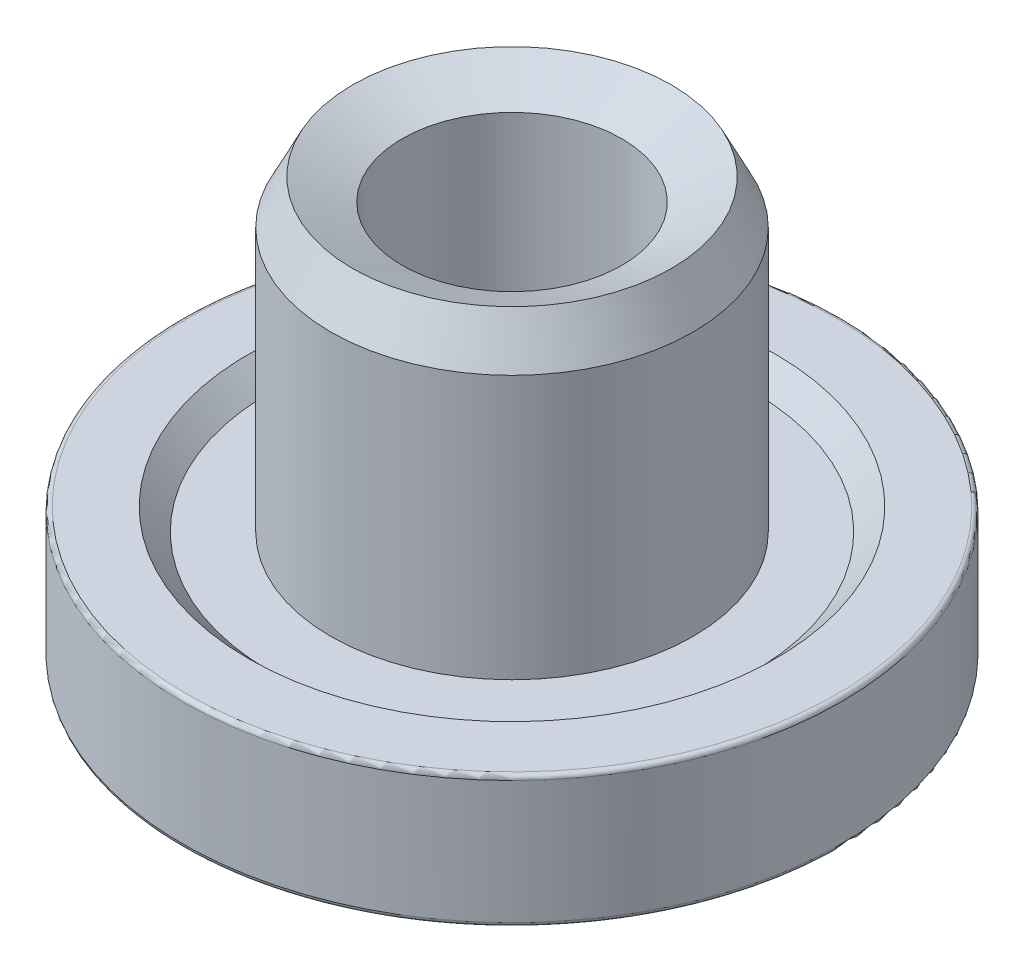
SolidWorks part; units mm, degrees
material "AISI 1020 Steel, Cold Rolled"
ref_plane "Front Plane" through (0, 0, 0) normal (0, 0, 1) x (1, 0, 0)
ref_plane "Top Plane" through (0, 0, 0) normal (0, 1, 0) x (1, 0, 0)
ref_plane "Right Plane" through (0, 0, 0) normal (1, 0, 0) x (0, 0, -1)
sketch "ProfileS" plane through (0, 0, 0) normal (0, 0, 1) x (1, 0, 0)
  line L0 (2.5, 0) -> (7.5, 0)
  line L1 (7.5, 0) -> (7.5, 3)
  line L2 (7.5, 3) -> (6, 3)
  line L3 (6, 3) -> (5.5, 2.5)
  line L4 (5.5, 2.5) -> (4.125, 2.5)
  line L5 (4.125, 2.5) -> (4.125, 8.5)
  line L6 (4.125, 8.5) -> (3.625, 9.5)
  line L7 (3.625, 9.5) -> (2.5, 9)
  line L8 (2.5, 9) -> (2.5, 0)
  line L9 (0, 0) -> (2.5, 0) construction
  line L10 (0, 0) -> (0, 9) construction
  line L11 (0, 9) -> (2.5, 9) construction
other "AlignGroup1" parameters "D1"=0, "HeadHeight"=3, "D3"=10, "PinBodyHeight"=8.5, "D5"=63.2472, "D6"=59.7326, "HeadDiameterInnerChamferHeight"=0.5, "PinBodyOuterChamferHeight"=1, "BoreDiameter"=5, "D7"=6, "PinBodyDiameter"=8.25, "D8"=3, "HeadDiameter"=15, "D9"=0.9107, "HeadDiameterBottomWidthControl"=1.5, "D10"=0.0939, "HeadDiameterInnerChamferWidth"=0.5, "D11"=0.8235, "PinBodyInnerChamferHeight"=0.5, "D12"=0.5439, "PinBodyOuterChamferWidth"=0.5
revolve "Profile" add sketch "ProfileS" angle 360 about L10
fillet "HeadFillet" radius 0.1 2 edges at (0, 3, -7.5) (0, 0, -7.5)
